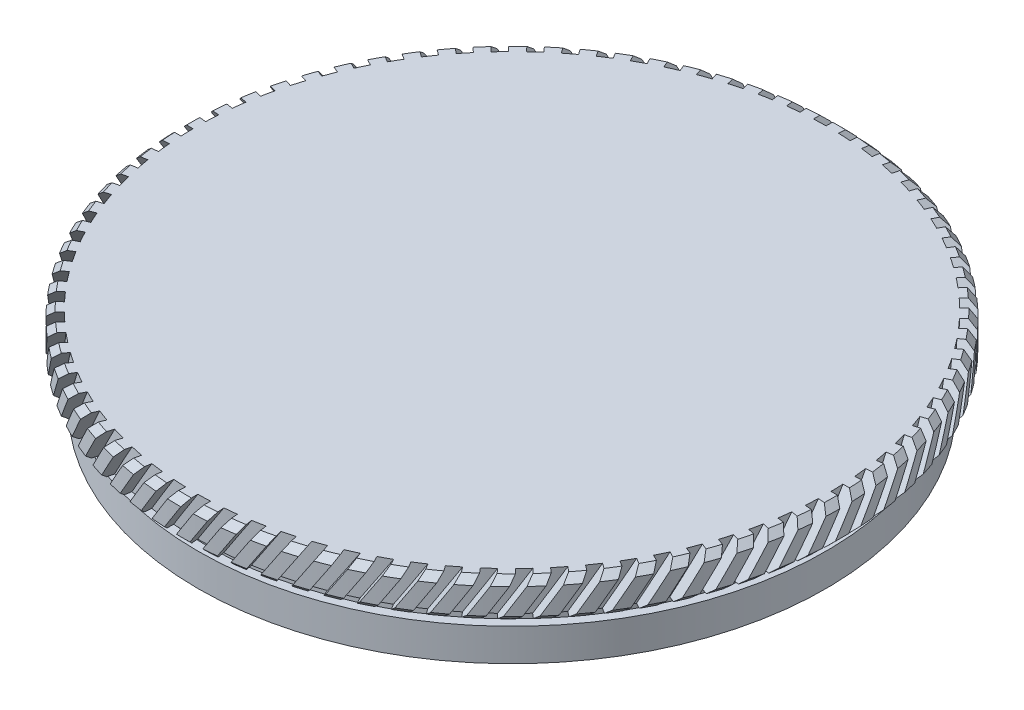
SolidWorks part; units mm, degrees
ref_plane "前视基准面" through (0, 0, 0) normal (0, 0, 1) x (1, 0, 0)
ref_plane "上视基准面" through (0, 0, 0) normal (0, 1, 0) x (1, 0, 0)
ref_plane "右视基准面" through (0, 0, 0) normal (1, 0, 0) x (0, 0, -1)
sketch "草图1" plane through (0, 0, 0) normal (0, 0, 1) x (1, 0, 0)
  line L0 (0, 66.6288) -> (0, -106.6399) construction
  line L1 (-97.6622, 0) -> (93.4292, 0) construction
  line L2 (0, 21.8713) -> (25.4, 21.8713)
  line L3 (25.4, 21.8713) -> (25.4, 18.8713)
  line L4 (23.5, 18.8713) -> (23.5, 17.8713)
  line L5 (23.5, 18.8713) -> (25.4, 18.8713)
  line L6 (24.2, 17.8713) -> (24.2, 15.3713)
  line L7 (23.5, 17.8713) -> (24.2, 17.8713)
  line L8 (21, 18.8713) -> (21, 15.3713)
  line L9 (0, 21.8713) -> (0, 18.8713)
  line L10 (21, 15.3713) -> (24.2, 15.3713)
  line L11 (0, 18.8713) -> (21, 18.8713)
  dimension "D1" = 25.4
  dimension "D2" = 3
  dimension "D3" = 23.5
  dimension "D4" = 24.2
  dimension "D5" = 21
  dimension "D6" = 1
  dimension "D7" = 2.5
revolve "旋转2" add sketch "草图1" angle 360 about L0
cosmetic thread "装饰螺纹线1" parameters "D2"=48
chamfer "倒角1" distance 0.5 angle 45 2 edges at (0, 21.8713, 25.4) (0, 18.8713, 25.4)
sketch "草图2" plane through (0, 0, 0) normal (0, 0, 1) x (1, 0, 0)
  line L0 (1.1082, 23.3033) -> (-5.3395, 13.2735)
  line L1 (1.1082, 23.3033) -> (1.7811, 22.8706)
  line L2 (-5.3395, 13.2735) -> (-4.6666, 12.8409)
  line L3 (1.7811, 22.8706) -> (-4.6666, 12.8409)
  dimension "D1" = 0.8
surface "曲面-等距1" parameters "D1"=1
extrude "切除-拉伸1" cut sketch "草图2" against normal up to surface (5.6252 mm away) from offset 30
delete or keep bodies "实体-删除/保留 1" type delete bodies bodies 107
pattern_circular "阵列(圆周)2" count 80 over 360 about axis through (0, 0, 0) along (0, 1, 0) of "切除-拉伸1"
